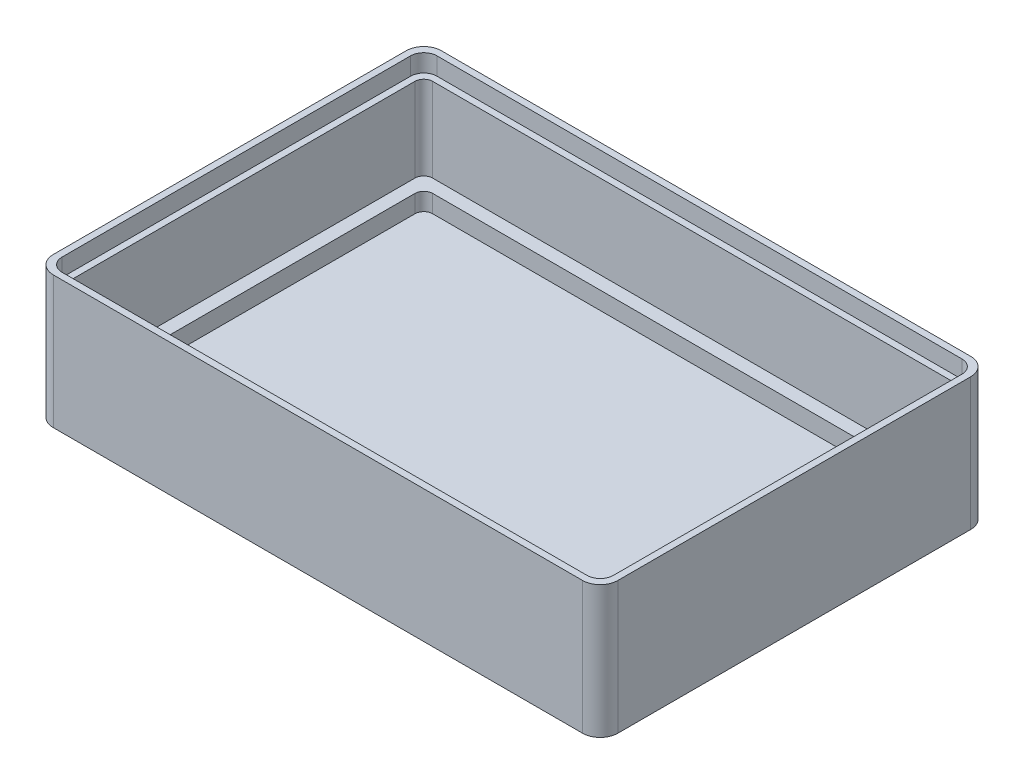
SolidWorks part; units mm, degrees
ref_plane "Front Plane" through (0, 0, 0) normal (0, 0, 1) x (1, 0, 0)
ref_plane "Top Plane" through (0, 0, 0) normal (0, 1, 0) x (1, 0, 0)
ref_plane "Right Plane" through (0, 0, 0) normal (1, 0, 0) x (0, 0, -1)
sketch "Sketch1" plane through (0, 0, 0) normal (0, 1, 0) x (1, 0, 0)
  line L1 (0, 44) -> (64, 44)
  line L2 (0, 44) -> (0, 0)
  line L3 (0, 0) -> (64, 0)
  line L4 (64, 44) -> (64, 0)
  point P4 (0, 0)
  dimension "D1" = 64
  dimension "D2" = 44
extrude "Boss-Extrude1" add sketch "Sketch1" along normal blind 15
sketch "Sketch2" plane through (0, 15, 0) normal (0, 1, 0) x (1, 0, 0)
  line L0 (0, 44) -> (0, 0) construction
  line L1 (62.5, 42.5) -> (1.5, 42.5)
  line L2 (62.5, 42.5) -> (62.5, 1.5)
  line L3 (62.5, 1.5) -> (1.5, 1.5)
  line L4 (1.5, 42.5) -> (1.5, 1.5)
  line L5 (0, 0) -> (64, 0) construction
  dimension "D1" = 61
  dimension "D2" = 41
  dimension "D3" = 1.5
  dimension "D4" = 1.5
extrude "Cut-Extrude1" cut sketch "Sketch2" against normal blind 13.5
sketch "Sketch3" plane through (0, 1.5, 0) normal (0, 1, 0) x (1, 0, 0)
  line L1 (61.0041, 41) -> (3.0041, 41)
  line L2 (61.0041, 41) -> (61.0041, 3)
  line L3 (61.0041, 3) -> (3.0041, 3)
  line L4 (3.0041, 41) -> (3.0041, 3)
  line L5 (62.5, 42.5) -> (1.5, 42.5)
  line L6 (62.5, 42.5) -> (62.5, 1.5)
  line L7 (62.5, 1.5) -> (1.5, 1.5)
  line L8 (1.5, 42.5) -> (1.5, 1.5)
  point P10 (3.0041, 2.9888)
  dimension "D1" = 58
  dimension "D2" = 38
  dimension "D3" = 1.5
  dimension "D4" = 1.4959
extrude "Boss-Extrude2" add sketch "Sketch3" along normal blind 2
fillet "Fillet1" radius 1 8 edges at (61.0041, 2.5, -3) (61.0041, 2.5, -41) (3.0041, 2.5, -3) (3.0041, 2.5, -41) (62.5, 9.25, -1.5) (62.5, 9.25, -42.5) (1.5, 9.25, -1.5) (1.5, 9.25, -42.5)
fillet "Fillet2" radius 2 4 edges at (64, 7.5, -44) (64, 7.5, 0) (0, 7.5, 0) (0, 7.5, -44)
sketch "Sketch4" plane through (0, 15, 0) normal (0, 1, 0) x (1, 0, 0)
  line L0 (61.5, 42.5) -> (2.5, 42.5) construction
  line L1 (62.5, 2.5) -> (62.5, 41.5) construction
  line L2 (2.5, 1.5) -> (61.5, 1.5) construction
  line L3 (1.5, 41.5) -> (1.5, 2.5) construction
  line L4 (61.5, 42.5) -> (2.5, 42.5)
  line L5 (62.5, 2.5) -> (62.5, 41.5)
  line L6 (2.5, 1.5) -> (61.5, 1.5)
  line L7 (1.5, 41.5) -> (1.5, 2.5)
  line L9 (2.25, 43.25) -> (61.75, 43.25)
  line L10 (0.75, 41.75) -> (0.75, 2.25)
  line L11 (2.25, 0.75) -> (61.75, 0.75)
  line L12 (63.25, 41.75) -> (63.25, 2.25)
  arc A0 (2.5, 42.5) -> (1.5, 41.5) centre (2.5, 41.5) ccw construction
  arc A1 (62.5, 41.5) -> (61.5, 42.5) centre (61.5, 41.5) ccw construction
  arc A2 (61.5, 1.5) -> (62.5, 2.5) centre (61.5, 2.5) ccw construction
  arc A3 (1.5, 2.5) -> (2.5, 1.5) centre (2.5, 2.5) ccw construction
  arc A4 (2.5, 42.5) -> (1.5, 41.5) centre (2.5, 41.5) ccw
  arc A5 (62.5, 41.5) -> (61.5, 42.5) centre (61.5, 41.5) ccw
  arc A6 (61.5, 1.5) -> (62.5, 2.5) centre (61.5, 2.5) ccw
  arc A7 (1.5, 2.5) -> (2.5, 1.5) centre (2.5, 2.5) ccw
  arc A8 (2.25, 0.75) -> (0.75, 2.25) centre (2.25, 2.25) cw
  arc A9 (61.75, 0.75) -> (63.25, 2.25) centre (61.75, 2.25) ccw
  arc A10 (63.25, 41.75) -> (61.75, 43.25) centre (61.75, 41.75) ccw
  arc A11 (2.25, 43.25) -> (0.75, 41.75) centre (2.25, 41.75) ccw
  dimension "D5" = 1.5
  dimension "D6" = 1.5
  dimension "D1" = 0.75
  dimension "D2" = 0.75
  dimension "D3" = 0.75
  dimension "D4" = 0.75
extrude "Cut-Extrude2" cut sketch "Sketch4" against normal blind 2
